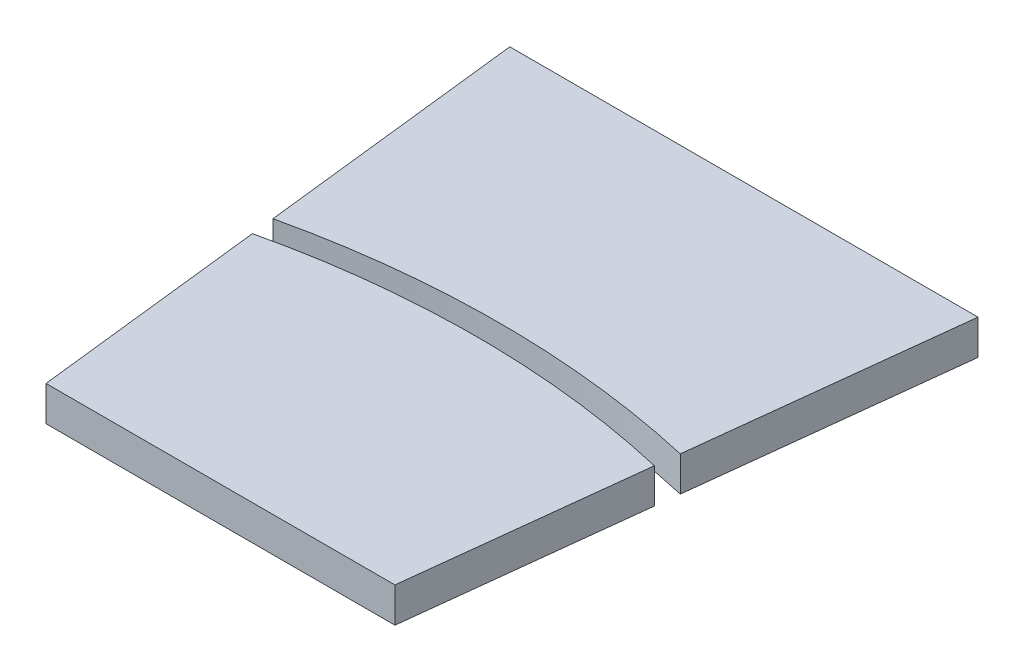
SolidWorks part; units mm, degrees
ref_plane "Front Plane" through (0, 0, 0) normal (0, 0, 1) x (1, 0, 0)
ref_plane "Top Plane" through (0, 0, 0) normal (0, 1, 0) x (1, 0, 0)
ref_plane "Right Plane" through (0, 0, 0) normal (1, 0, 0) x (0, 0, -1)
sketch "Sketch1" plane through (0, 0, 0) normal (0, 1, 0) x (1, 0, 0)
  line L0 (-20.1271, 99.5) -> (-15, 54.5)
  line L5 (-20.1271, 99.5) -> (0, 99.5)
  line L6 (0, 99.5) -> (0, 54.5)
  line L7 (0, 54.5) -> (-15, 54.5)
  point P4 (0, 77)
  dimension "D1" = 45
  dimension "D2" = 77
  dimension "D3" = 6.5
  dimension "D4" = 15
extrude "Boss-Extrude1" add sketch "Sketch1" along normal blind 3
mirror "Mirror2" about plane through (0, 0, 0) normal (1, 0, 0) of "Boss-Extrude1"
sketch "Sketch2" plane through (0, 3, 0) normal (0, 1, 0) x (1, 0, 0)
  line L0 (-20.1271, 99.5) -> (-15, 54.5) construction
  line L1 (20.1271, 99.5) -> (15, 54.5) construction
  line L2 (-17.2813, 74.5225) -> (-17.5091, 76.5224)
  line L3 (17.2813, 74.5225) -> (17.5091, 76.5224)
  arc A0 (-17.2813, 74.5225) -> (17.2813, 74.5225) centre (0, 0) cw
  arc A1 (-17.5091, 76.5224) -> (17.5091, 76.5224) centre (0, 0) cw
  dimension "D1" = 76.5
  dimension "D2" = 78.5
extrude "Cut-Extrude1" cut sketch "Sketch2" against normal through all both and the other way through all
